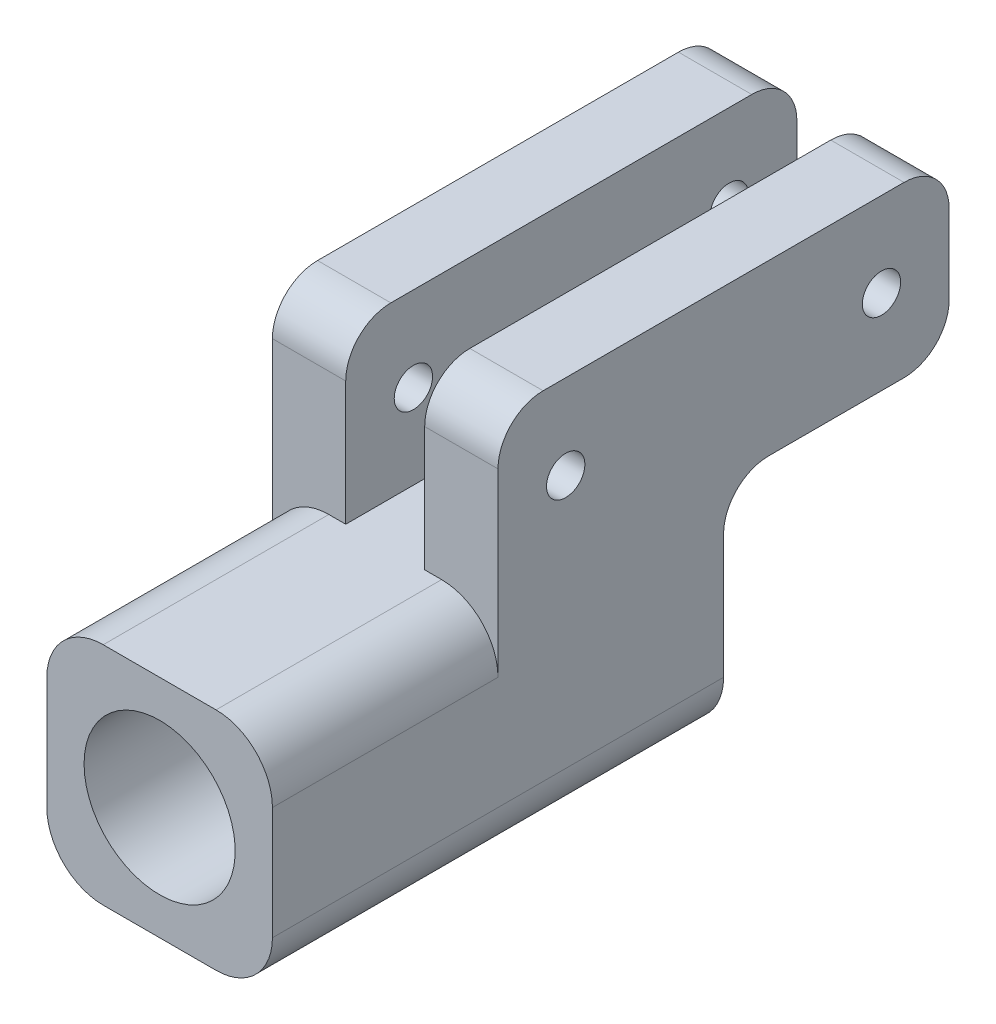
SolidWorks part; units mm, degrees
ref_plane "Alzado" through (0, 0, 0) normal (0, 0, 1) x (1, 0, 0)
ref_plane "Planta" through (0, 0, 0) normal (0, 1, 0) x (1, 0, 0)
ref_plane "Vista lateral" through (0, 0, 0) normal (1, 0, 0) x (0, 0, -1)
sketch "Croquis1" plane through (0, 0, 0) normal (0, 1, 0) x (1, 0, 0)
  line L1 (-10, -20) -> (10, -20)
  line L2 (-10, -20) -> (-10, 20)
  line L3 (-10, 20) -> (10, 20)
  line L4 (10, -20) -> (10, 20)
  line L5 (-10, -20) -> (10, 20) construction
  line L6 (-10, 20) -> (10, -20) construction
  point P0 (0, 0)
  dimension "D1" = 20
  dimension "D2" = 40
extrude "Saliente-Extruir1" add sketch "Croquis1" along normal mid plane 20
sketch "Croquis5" plane through (0, 0, -20) normal (0, 0, -1) x (-1, 0, 0)
  circle A0 centre (0, 0) radius 6.7
  dimension "D1" = 13.4
extrude "Cortar-Extruir1" cut sketch "Croquis5" against normal up to surface (40 mm away) up to face at (0, 0, 20)
sketch "Croquis6" plane through (0, 0, 0) normal (1, 0, 0) x (0, 0, -1)
  line L0 (0, 10) -> (0, 25)
  line L1 (-20, 10) -> (20, 10) construction
  line L2 (0, 25) -> (40, 25)
  line L3 (40, 25) -> (40, 10)
  line L4 (40, 10) -> (0, 10)
  dimension "D1" = 15
  dimension "D2" = 40
extrude "Saliente-Extruir2" add sketch "Croquis6" along normal mid plane 20
sketch "Croquis7" plane through (0, 25, 0) normal (0, 1, 0) x (1, 0, 0)
  line L0 (3.5, 0) -> (3.5, 40)
  line L1 (10, 0) -> (-10, 0) construction
  line L2 (10, 40) -> (-10, 40) construction
  line L3 (3.5, 40) -> (-3.5, 40)
  line L4 (-3.5, 40) -> (-3.5, 0)
  line L5 (10, 0) -> (-10, 0) construction
  line L6 (-3.5, 0) -> (3.5, 0)
  line L7 (0, -20) -> (0, 42.0836) construction
  line L8 (-10, -20) -> (10, -20) construction
  point P14 (0, 0)
  dimension "D1" = 7
extrude "Cortar-Extruir2" cut sketch "Croquis7" against normal up to surface (15 mm away) up to face at (0, 10, -30)
sketch "Croquis8" plane through (10, 0, 0) normal (1, 0, 0) x (0, 0, -1)
  line L0 (0, 17.5) -> (40, 17.5) construction
  line L1 (0, 25) -> (0, 10) construction
  line L3 (20, 17.5) -> (20, 21.2852) construction
  circle A0 centre (6, 17.5) radius 1.7
  circle A3 centre (34, 17.5) radius 1.7
  dimension "D1" = 3.4
  dimension "D2" = 6
  dimension "D4" = 40
extrude "Cortar-Extruir3" cut sketch "Croquis8" against normal up to surface (20 mm away) up to face at (-10, 8.75, -10)
fillet "Redondeo1" radius 4 8 edges at (6.75, 25, 0) (-6.75, 25, 0) (-6.75, 10, -40) (-6.75, 25, -40) (6.75, 25, -40) (6.75, 10, -40) (-6.75, 10, -20) (6.75, 10, -20)
fillet "Redondeo2" radius 5 4 edges at (-10, 10, 10) (10, 10, 10) (-10, -10, 0) (10, -10, 0)
